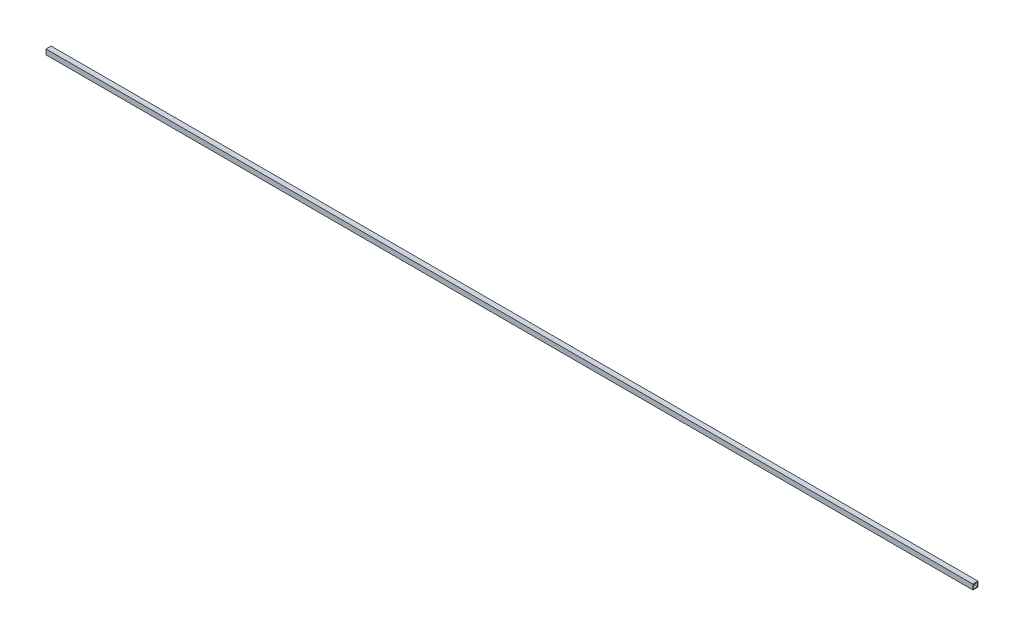
SolidWorks part; units mm, degrees
material "AISI 316 Stainless Steel Sheet (SS)"
ref_plane "Plan de face" through (0, 0, 0) normal (0, 0, 1) x (1, 0, 0)
ref_plane "Plan de dessus" through (0, 0, 0) normal (0, 1, 0) x (1, 0, 0)
ref_plane "Plan de droite" through (0, 0, 0) normal (1, 0, 0) x (0, 0, -1)
sketch "crossmember length" plane through (0, 0, 0) normal (0, 0, 1) x (1, 0, 0)
  line L0 (0, 0) -> (9206.23, 0)
  dimension "D1" = 9206.23
other "Al tube square AL TUBE 2 SQR X 0.25 WALL(1)"
ref_plane "Plane1" through (0, 0, 0) normal (1, 0, 0) x (0, 1, 0)
sketch "Sketch1" plane through (0, 0, 0) normal (1, 0, 0) x (0, 1, 0)
  line L0 (-19.05, -19.05) -> (-19.05, 19.05)
  line L1 (19.05, 19.05) -> (-19.05, 19.05)
  line L2 (19.05, 19.05) -> (19.05, -19.05)
  line L3 (-19.05, -19.05) -> (19.05, -19.05)
  line L4 (-25.4, -25.4) -> (25.4, -25.4)
  line L5 (-25.4, -25.4) -> (-25.4, 25.4)
  line L6 (25.4, 25.4) -> (-25.4, 25.4)
  line L7 (25.4, 25.4) -> (25.4, -25.4)
  line L8 (0, -19.05) -> (0, -25.4) construction
  line L9 (0, -19.05) -> (0, 19.05) construction
  line L10 (0, 19.05) -> (0, 25.4) construction
  line L11 (25.4, 0) -> (19.05, 0) construction
  line L12 (19.05, 0) -> (-19.05, 0) construction
  line L13 (-19.05, 0) -> (-25.4, 0) construction
  point P14 (0, 0)
  point P17 (0, 0)
  dimension "Thickness" = 6.35
  dimension "V_leg" = 50.8
  dimension "H_leg" = 50.8
equation "\"crossmember_w\"= 2in"
equation "\"crossmember_h\"= 2in"
equation "\"crossmember_l\"= 362.45in"
equation "\"D1@crossmember length\"=\"crossmember_l\""
